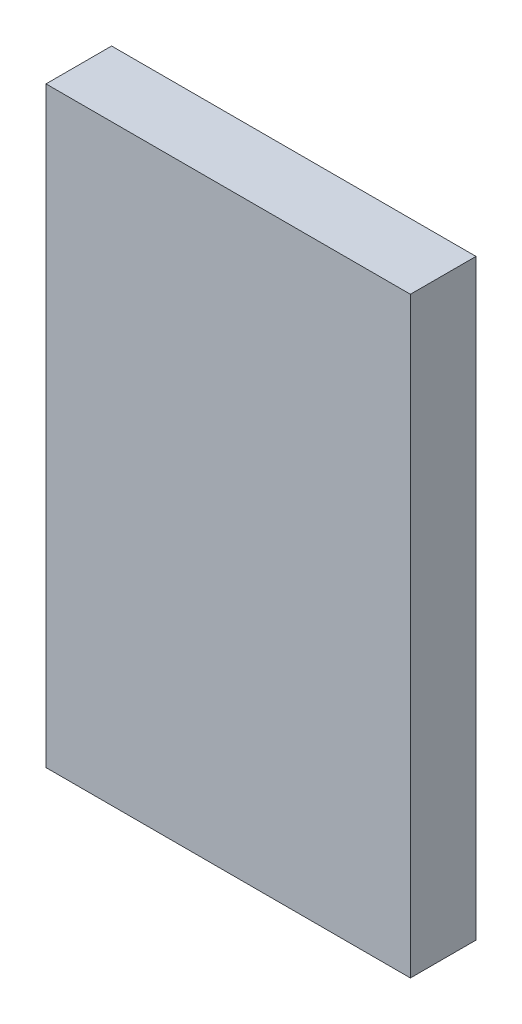
SolidWorks part; units mm, degrees
ref_plane "Front Plane" through (0, 0, 0) normal (1, 0, 0) x (0, 1, 0)
ref_plane "Top Plane" through (0, 0, 0) normal (0, 0, 1) x (0, 1, 0)
ref_plane "Right Plane" through (0, 0, 0) normal (0, 1, 0) x (-1, 0, 0)
sketch "Sketch1" plane through (0, 0, 0) normal (0, 0, 1) x (0, 1, 0)
  line L1 (0, 0) -> (65, 0)
  line L2 (0, 0) -> (0, 40)
  line L3 (0, 40) -> (65, 40)
  line L4 (65, 0) -> (65, 40)
  dimension "D1" = 65
  dimension "D2" = 40
extrude "Boss-Extrude1" add sketch "Sketch1" along normal blind 7.2
